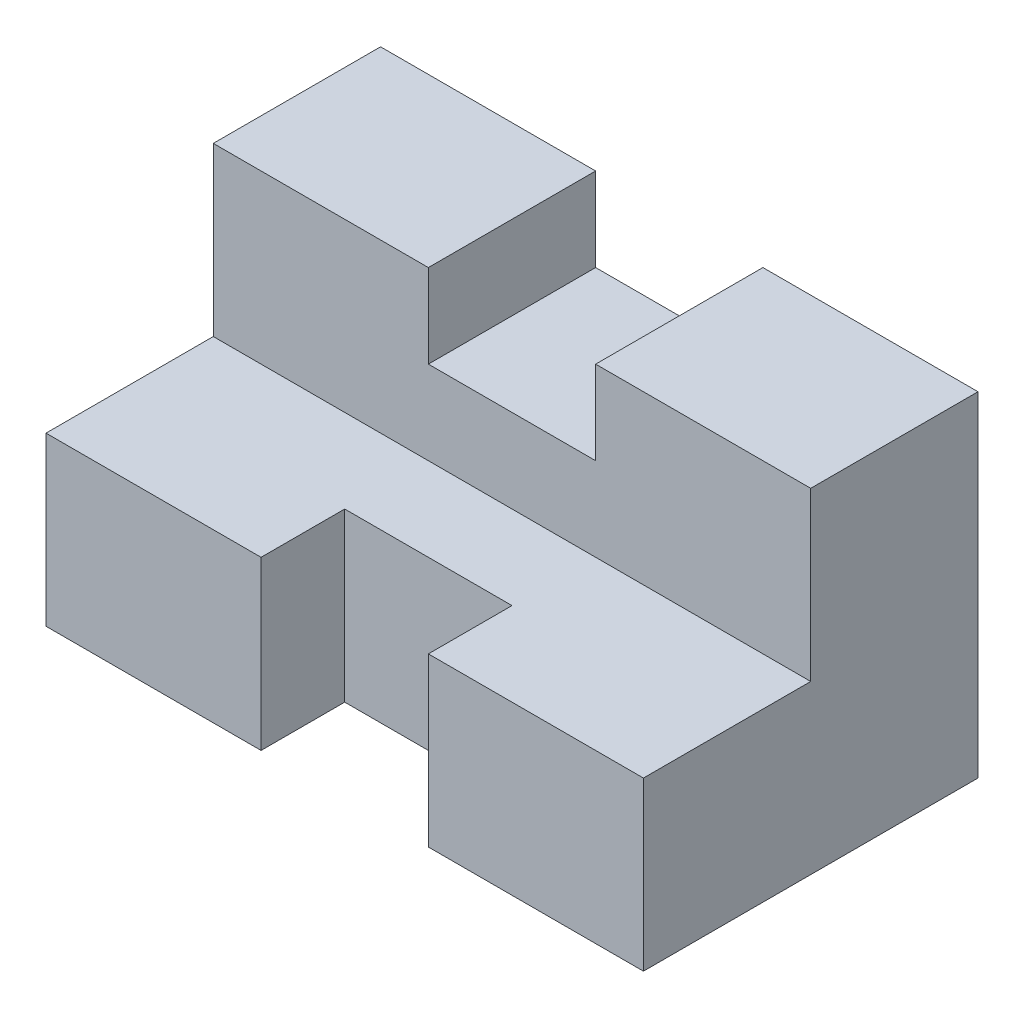
SolidWorks part; units mm, degrees
material "회주철"
ref_plane "정면" through (0, 0, 0) normal (0, 0, 1) x (1, 0, 0)
ref_plane "윗면" through (0, 0, 0) normal (0, 1, 0) x (1, 0, 0)
ref_plane "우측면" through (0, 0, 0) normal (1, 0, 0) x (0, 0, -1)
sketch "스케치1" plane through (0, 0, 0) normal (1, 0, 0) x (0, 0, -1)
  line L0 (0, 0) -> (28, 0)
  line L1 (28, 0) -> (28, 28)
  line L2 (28, 28) -> (14, 28)
  line L3 (14, 28) -> (14, 14)
  line L4 (14, 14) -> (0, 14)
  line L5 (0, 14) -> (0, 0)
  dimension "D1" = 28
  dimension "D2" = 14
  dimension "D3" = 14
  dimension "D4" = 28
extrude "보스-돌출1" add sketch "스케치1" along normal mid plane 50
sketch "스케치2" plane through (0, 0, 0) normal (0, 1, 0) x (1, 0, 0)
  line L1 (7, 7) -> (-7, 7)
  line L2 (-7, 7) -> (-7, 0)
  line L3 (-7, 0) -> (7, 0)
  line L4 (7, 0) -> (7, 7)
  dimension "D1" = 7
  dimension "D2" = 14
  dimension "D3" = 7
extrude "컷-돌출1" cut sketch "스케치2" along normal up to next
sketch "스케치3" plane through (0, 0, 0) normal (0, 0, 1) x (1, 0, 0)
  line L0 (-7, 21) -> (-7, 28)
  line L1 (7, 21) -> (7, 28)
  line L2 (25, 28) -> (-25, 28) construction
  line L3 (7, 28) -> (-7, 28)
  line L4 (7, 21) -> (-7, 21)
  line L5 (25, 28) -> (-25, 28) construction
  line L6 (25, 21) -> (-25, 21) construction
  point P1 (0, 0)
  dimension "D1" = 21
  dimension "D2" = 14
  dimension "D3" = 7
extrude "컷-돌출2" cut sketch "스케치3" against normal through all
